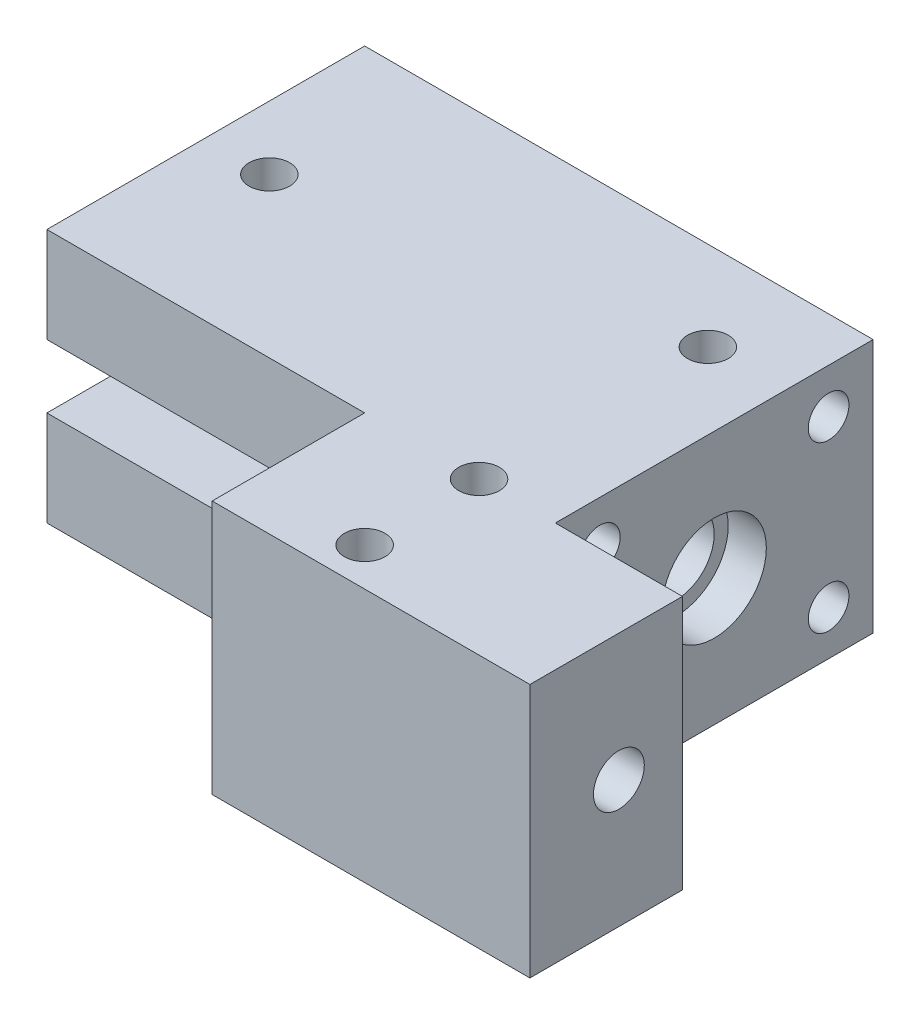
SolidWorks part; units mm, degrees
ref_plane "Спереди" through (0, 0, 0) normal (0, 0, 1) x (1, 0, 0)
ref_plane "Сверху" through (0, 0, 0) normal (0, 1, 0) x (1, 0, 0)
ref_plane "Справа" through (0, 0, 0) normal (1, 0, 0) x (0, 0, -1)
sketch "Эскиз1" plane through (0, 0, 0) normal (0, 1, 0) x (1, 0, 0)
  line L1 (20, -12.5) -> (-20, -12.5)
  line L2 (20, -12.5) -> (20, 12.5)
  line L3 (20, 12.5) -> (-20, 12.5)
  line L4 (-20, -12.5) -> (-20, 12.5)
  line L5 (20, -12.5) -> (-20, 12.5) construction
  line L6 (20, 12.5) -> (-20, -12.5) construction
  point P0 (0, 0)
  dimension "D1" = 25
  dimension "D2" = 40
extrude "Бобышка-Вытянуть1" add sketch "Эскиз1" along normal blind 20
sketch "Эскиз3" plane through (-20, 0, 0) normal (-1, 0, 0) x (0, 0, 1)
  line L0 (0, 20) -> (0, 0) construction
  line L1 (-12.5, 20) -> (12.5, 20) construction
  line L2 (-12.5, 0) -> (12.5, 0) construction
  circle A0 centre (0, 10) radius 3
extrude "Вырез-Вытянуть2" cut sketch "Эскиз3" against normal through all
sketch "Эскиз2" plane through (-20, 0, 0) normal (-1, 0, 0) x (0, 0, 1)
  line L0 (-12.5, 20) -> (12.5, 0) construction
  circle A0 centre (0, 10) radius 4.1
extrude "Вырез-Вытянуть1" cut sketch "Эскиз2" against normal blind 26
sketch "Эскиз4" plane through (-20, 0, 0) normal (1, 0, 0) x (0, 0, -1)
  line L0 (-12.5, 20) -> (-12.5, 0) construction
  line L1 (12.5, 7.5) -> (-12.5, 7.5)
  line L2 (12.5, 7.5) -> (12.5, 12.5)
  line L3 (12.5, 12.5) -> (-12.5, 12.5)
  line L4 (-12.5, 7.5) -> (-12.5, 12.5)
  line L5 (12.5, 7.5) -> (-12.5, 12.5) construction
  line L6 (12.5, 12.5) -> (-12.5, 7.5) construction
  point P0 (0, 10)
  dimension "D1" = 5
extrude "Вырез-Вытянуть3" cut sketch "Эскиз4" along normal blind 20
sketch "Эскиз5" plane through (20, 0, 0) normal (1, 0, 0) x (0, 0, -1)
  circle A0 centre (0, 10) radius 4.1
extrude "Вырез-Вытянуть4" cut sketch "Эскиз5" against normal blind 3
sketch "Эскиз6" plane through (0, 20, 0) normal (0, 1, 0) x (1, 0, 0)
  line L0 (-20, 0) -> (20, 0) construction
  line L1 (-20, 12.5) -> (-20, -12.5) construction
  line L2 (20, -12.5) -> (20, 12.5) construction
  circle A0 centre (-15, 0) radius 1.6
  dimension "D1" = 5
extrude "Вырез-Вытянуть5" cut sketch "Эскиз6" against normal through all
sketch "Эскиз7" plane through (-20, 0, 0) normal (-1, 0, 0) x (0, 0, 1)
  line L0 (-15, 16.5) -> (15, 16.5) construction
  line L3 (-15, 3.5) -> (15, 3.5) construction
  line L7 (0, 20) -> (0, 0) construction
  line L8 (-12.5, 20) -> (12.5, 20) construction
  line L9 (-12.5, 0) -> (12.5, 0) construction
  circle A0 centre (-9, 16.5) radius 1.6
  circle A1 centre (9, 16.5) radius 1.6
  circle A2 centre (-9, 3.5) radius 1.6
  circle A3 centre (9, 3.5) radius 1.6
  point P20 (0, 16.5)
  point P22 (0, 3.5)
  dimension "D1" = 18
  dimension "D2" = 9
  dimension "D3" = 18
  dimension "D4" = 9
  dimension "D5" = 3.5
  dimension "D6" = 3.5
extrude "Вырез-Вытянуть6" cut sketch "Эскиз7" against normal through all
sketch "Эскиз8" plane through (0, 0, 12.5) normal (0, 0, 1) x (1, 0, 0)
  line L1 (30, 20) -> (5, 20)
  line L2 (5, 20) -> (5, 0)
  line L3 (-20, 0) -> (20, 0) construction
  line L4 (5, 0) -> (30, 0)
  line L5 (30, 0) -> (30, 20)
  line L6 (20, 20) -> (20, 0) construction
  dimension "D1" = 25
  dimension "D2" = 15
  dimension "D3" = 20
extrude "Бобышка-Вытянуть2" add sketch "Эскиз8" along normal blind 12
sketch "Эскиз9" plane through (0, 20, 0) normal (0, 1, 0) x (1, 0, 0)
  line L0 (14, -24.5) -> (14, 12.5) construction
  line L1 (30, -24.5) -> (5, -24.5) construction
  line L2 (20, 12.5) -> (-20, 12.5) construction
  line L3 (20, -12.5) -> (20, 12.5) construction
  circle A0 centre (14, -21.5) radius 1.6
  circle A1 centre (14, 5.5) radius 1.6
  circle A2 centre (14, -12.5) radius 1.6
  dimension "D1" = 27
  dimension "D4" = 9
  dimension "D2" = 6
  dimension "D3" = 3
extrude "Вырез-Вытянуть7" cut sketch "Эскиз9" against normal through all
sketch "Эскиз10" plane through (5, 0, 0) normal (-1, 0, 0) x (0, 0, 1)
  line L0 (24.5, 10) -> (12.5, 10) construction
  line L1 (24.5, 20) -> (24.5, 0) construction
  line L2 (12.5, 20) -> (12.5, 0) construction
  circle A0 centre (17.5, 10) radius 2
  point P8 (0, 0)
  point P10 (-84.2174, 21.4777)
  dimension "D1" = 5
extrude "Вырез-Вытянуть8" cut sketch "Эскиз10" against normal through all
sketch "Эскиз12" plane through (-20, 0, 0) normal (-1, 0, 0) x (0, 0, 1)
  circle A0 centre (0, 10) radius 5
extrude "Вырез-Вытянуть9" cut sketch "Эскиз12" against normal blind 23
